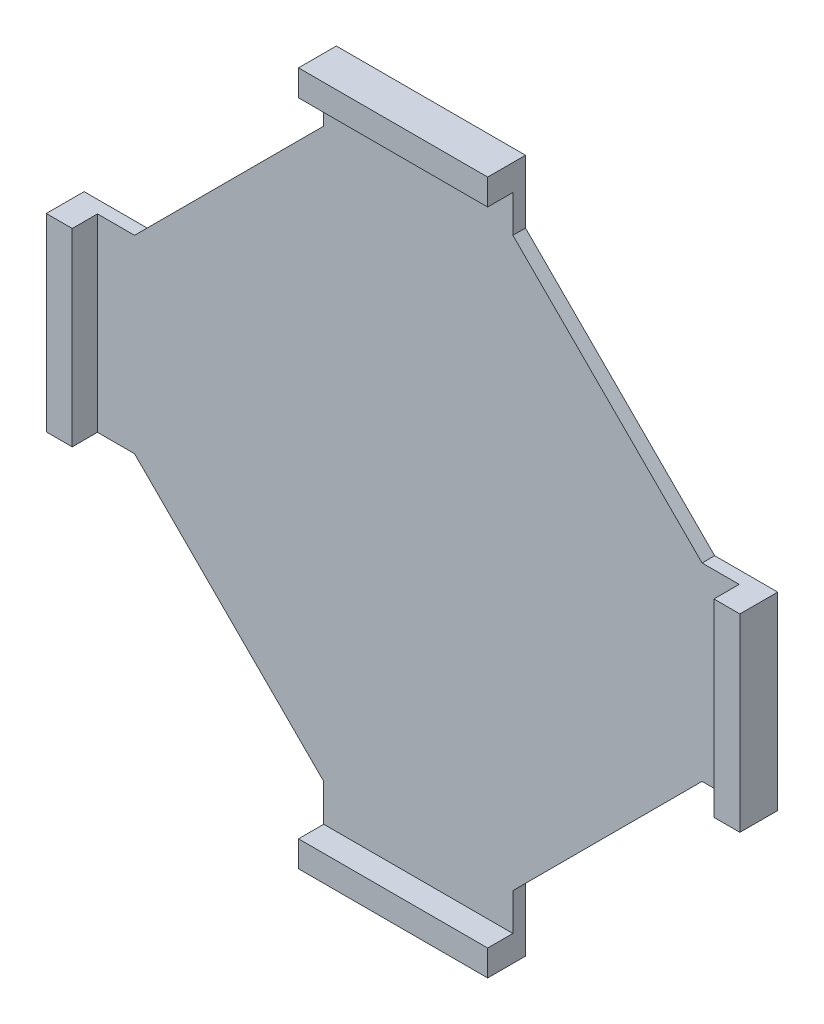
SolidWorks part; units mm, degrees
ref_plane "Front" through (0, 0, 0) normal (0, 0, 1) x (1, 0, 0)
ref_plane "Top" through (0, 0, 0) normal (0, 1, 0) x (1, 0, 0)
ref_plane "Right" through (0, 0, 0) normal (1, 0, 0) x (0, 0, -1)
sketch "Sketch1" plane through (0, 0, 0) normal (0, 0, 1) x (1, 0, 0)
  line L0 (57.15, 19.05) -> (69.85, 19.05)
  line L1 (19.05, -69.85) -> (-19.05, -69.85)
  line L2 (69.85, -19.05) -> (69.85, 19.05)
  line L4 (-69.85, -19.05) -> (-69.85, 19.05)
  line L5 (-19.05, 69.85) -> (19.05, 69.85)
  line L8 (19.05, 57.15) -> (19.05, 69.85)
  line L10 (-19.05, 57.15) -> (-19.05, 69.85)
  line L14 (57.15, -19.05) -> (69.85, -19.05)
  line L15 (19.05, -57.15) -> (19.05, -69.85)
  line L17 (-19.05, -57.15) -> (-19.05, -69.85)
  line L18 (-57.15, -19.05) -> (-69.85, -19.05)
  line L20 (-57.15, 19.05) -> (-69.85, 19.05)
  line L21 (-57.15, 19.05) -> (-19.05, 57.15)
  line L22 (19.05, 57.15) -> (57.15, 19.05)
  line L23 (57.15, -19.05) -> (19.05, -57.15)
  line L24 (-19.05, -57.15) -> (-57.15, -19.05)
  point P0 (0, 0)
  point P6 (0, 69.85)
  point P27 (0, 0)
  dimension "D5" = 4
extrude "Boss-Extrude1" add sketch "Sketch1" along normal blind 2.54
sketch "Sketch2" plane through (0, 0, 2.54) normal (0, 0, 1) x (1, 0, 0)
  line L0 (19.05, -69.85) -> (19.05, -57.15) construction
  line L1 (-19.05, -69.85) -> (19.05, -69.85)
  line L2 (-19.05, -69.85) -> (-19.05, -64.6203)
  line L3 (-19.05, -64.6203) -> (19.05, -64.6203)
  line L4 (19.05, -69.85) -> (19.05, -64.6203)
  line L5 (-69.85, 19.05) -> (-64.6203, 19.05)
  line L6 (-69.85, 19.05) -> (-69.85, -19.05)
  line L7 (-69.85, -19.05) -> (-64.6203, -19.05)
  line L8 (-64.6203, 19.05) -> (-64.6203, -19.05)
  line L9 (19.05, 69.85) -> (19.05, 64.6203)
  line L10 (19.05, 69.85) -> (-19.05, 69.85)
  line L11 (-19.05, 69.85) -> (-19.05, 64.6203)
  line L12 (19.05, 64.6203) -> (-19.05, 64.6203)
  line L13 (69.85, -19.05) -> (64.6203, -19.05)
  line L14 (69.85, -19.05) -> (69.85, 19.05)
  line L15 (69.85, 19.05) -> (64.6203, 19.05)
  line L16 (64.6203, -19.05) -> (64.6203, 19.05)
  point P22 (0, 0)
  dimension "D1" = 4
extrude "Boss-Extrude2" add sketch "Sketch2" along normal blind 5.08
